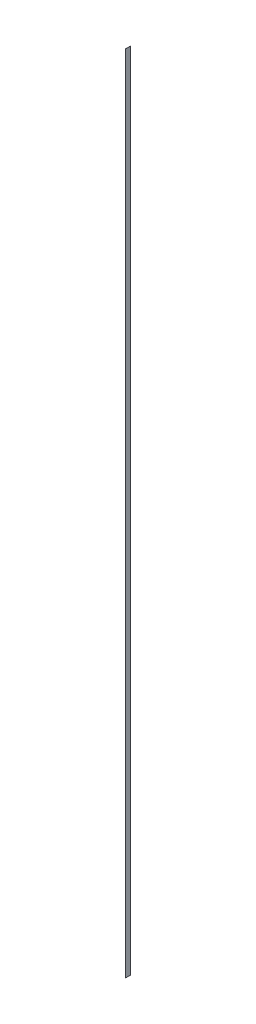
SolidWorks part; units mm, degrees
ref_plane "Front Plane" through (0, 0, 0) normal (0, 0, 1) x (1, 0, 0)
ref_plane "Top Plane" through (0, 0, 0) normal (0, 1, 0) x (1, 0, 0)
ref_plane "Right Plane" through (0, 0, 0) normal (1, 0, 0) x (0, 0, -1)
sketch "Sketch1" plane through (0, 0, 0) normal (1, 0, 0) x (0, 0, -1)
  line L1 (-25.4, 0) -> (25.4, 0)
  line L2 (-25.4, 0) -> (-25.4, 8229.6)
  line L3 (-25.4, 8229.6) -> (25.4, 8229.6)
  line L4 (25.4, 0) -> (25.4, 8229.6)
  dimension "D1" = 50.8
  dimension "D2" = 8229.6
extrude "Boss-Extrude1" add sketch "Sketch1" along normal blind 1.27
